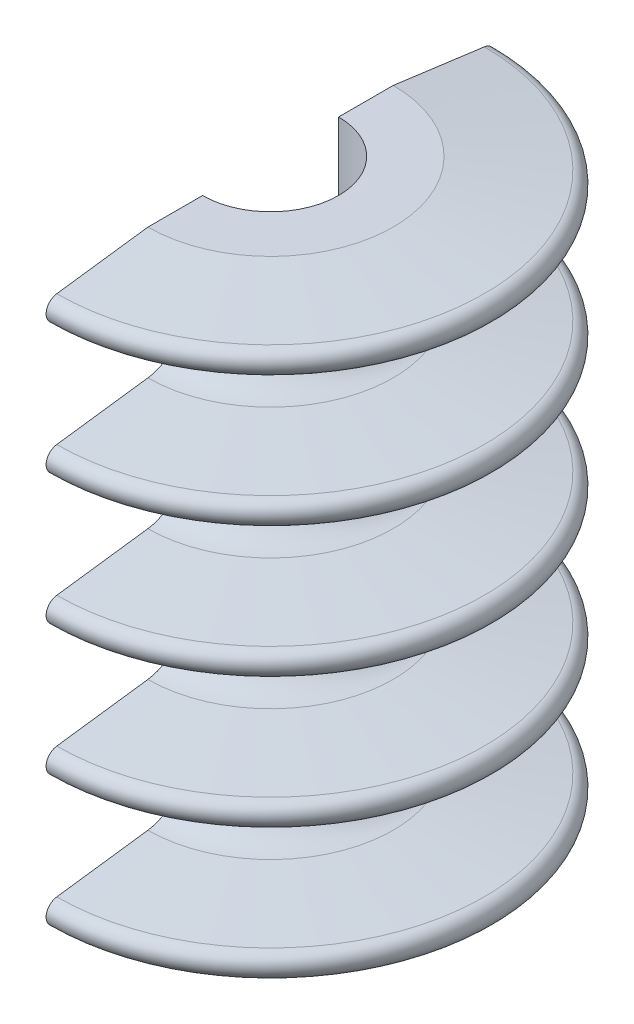
SolidWorks part; units mm, degrees
ref_plane "Front Plane" through (0, 0, 0) normal (0, 0, 1) x (1, 0, 0)
ref_plane "Top Plane" through (0, 0, 0) normal (0, 1, 0) x (1, 0, 0)
ref_plane "Right Plane" through (0, 0, 0) normal (1, 0, 0) x (0, 0, -1)
sketch "Sketch2" plane through (0, 0, 0) normal (0, 0, 1) x (1, 0, 0)
  line L0 (0, 47) -> (0, -47) construction
  line L1 (0, 47) -> (-20.2, 47) construction
  line L2 (-20.2, 47) -> (-35.2, 45)
  line L3 (-35.2, 45) -> (-35.2, 41) construction
  line L4 (-35.2, 41) -> (-20.2, 39)
  line L5 (-35.2, 43) -> (0, 43) construction
  line L6 (-20.2, 39) -> (-20.2, 25.5) construction
  line L7 (-20.2, 25.5) -> (-35.2, 23.5)
  line L8 (-20.2, 47) -> (-11.2, 47)
  line L9 (-35.2, 23.5) -> (-35.2, 19.5) construction
  line L10 (-35.2, 19.5) -> (-20.2, 17.5)
  line L11 (-20.2, 17.5) -> (-20.2, 4) construction
  line L12 (-20.2, 4) -> (-35.2, 2)
  line L13 (-20.2, -47) -> (-11.2, -47)
  line L14 (-35.2, 2) -> (-35.2, -2) construction
  line L15 (-35.2, -2) -> (-20.2, -4)
  line L16 (-20.2, -4) -> (-20.2, -17.5) construction
  line L17 (-20.2, -17.5) -> (-35.2, -19.5)
  line L18 (-11.2, 47) -> (-11.2, -47)
  line L19 (-35.2, -19.5) -> (-35.2, -23.5) construction
  line L20 (-35.2, -23.5) -> (-20.2, -25.5)
  line L21 (-20.2, -25.5) -> (-20.2, -39) construction
  line L22 (-20.2, -39) -> (-35.2, -41)
  line L24 (-35.2, -41) -> (-35.2, -45) construction
  line L25 (-35.2, -45) -> (-20.2, -47)
  line L27 (-20.2, -47) -> (0, -47) construction
  line L28 (0, 25.5) -> (-20.2, 25.5) [skipped]
  line L29 (0, 4) -> (-20.2, 4) [skipped]
  line L30 (0, -17.5) -> (-20.2, -17.5) [skipped]
  line L31 (0, -39) -> (-20.2, -39) [skipped]
  line L32 (-20.2, -47) -> (-20.2, -60.5) construction
  arc A0 (-35.2, 45) -> (-35.2, 41) centre (-34.9333, 43) ccw
  arc A1 (-20.2, 39) -> (-20.2, 25.5) centre (-21.1, 32.25) cw
  arc A2 (-35.2, 23.5) -> (-35.2, 19.5) centre (-34.9333, 21.5) ccw
  arc A3 (-20.2, 17.5) -> (-20.2, 4) centre (-21.1, 10.75) cw
  arc A4 (-35.2, 2) -> (-35.2, -2) centre (-34.9333, 0) ccw
  arc A5 (-20.2, -4) -> (-20.2, -17.5) centre (-21.1, -10.75) cw
  arc A6 (-35.2, -19.5) -> (-35.2, -23.5) centre (-34.9333, -21.5) ccw
  arc A7 (-20.2, -25.5) -> (-20.2, -39) centre (-21.1, -32.25) cw
  arc A8 (-35.2, -41) -> (-35.2, -45) centre (-34.9333, -43) ccw
  arc A10 (-20.2, -47) -> (-20.2, -60.5) centre (-21.1, -53.75) cw [skipped]
  point P4 (0, 0)
  point P43 (-20.2, 32.25)
  dimension "D1" = 94
  dimension "D2" = 11.2
  dimension "D3" = 15
  dimension "D4" = 4
  dimension "D5" = 4
  dimension "D6" = 5
  dimension "D8" = 9
  dimension "7" = 4
  dimension "D10" = 9
  dimension "D9" = 5
revolve "Revolve1" add sketch "Sketch2" angle 360 about L0
sketch "Sketch3" plane through (0, -47, 0) normal (0, -1, 0) x (1, 0, 0)
  line L1 (0, -55.1346) -> (-63.7941, -55.1346)
  line L2 (0, -55.1346) -> (0, 55.0005)
  line L3 (0, 55.0005) -> (-63.7941, 55.0005)
  line L4 (-63.7941, -55.1346) -> (-63.7941, 55.0005)
extrude "Cut-Extrude1" cut sketch "Sketch3" against normal up to surface (94 mm away) up to face at (-11.2, 47, 0)
sketch "Sketch4" plane through (0, 0, 0) normal (1, 0, 0) x (0, 0, -1)
  circle A0 centre (0, -32.25) radius 1.7
  circle A1 centre (0, 32.25) radius 1.7
  arc A2 (-20.2, -39) -> (-20.2, -25.5) centre (-21.1, -32.25) ccw construction
  arc A3 (-20.2, 25.5) -> (-20.2, 39) centre (-21.1, 32.25) ccw construction
  point P11 (-14.2903, -32.25)
  point P16 (-14.2903, 32.25)
  dimension "D1" = 3.4
extrude "Cut-Extrude2" cut sketch "Sketch4" along normal through all
ref_plane "Plane1" through (17, 0, 0) normal (1, 0, 0) x (0, 0, -1)
sketch "Sketch5" plane through (17, 0, 0) normal (1, 0, 0) x (0, 0, -1)
  circle A0 centre (0, -32.25) radius 2.95
  circle A1 centre (0, 32.25) radius 2.95
  dimension "D1" = 5.9
extrude "Cut-Extrude3" cut sketch "Sketch5" against normal blind 3.8
